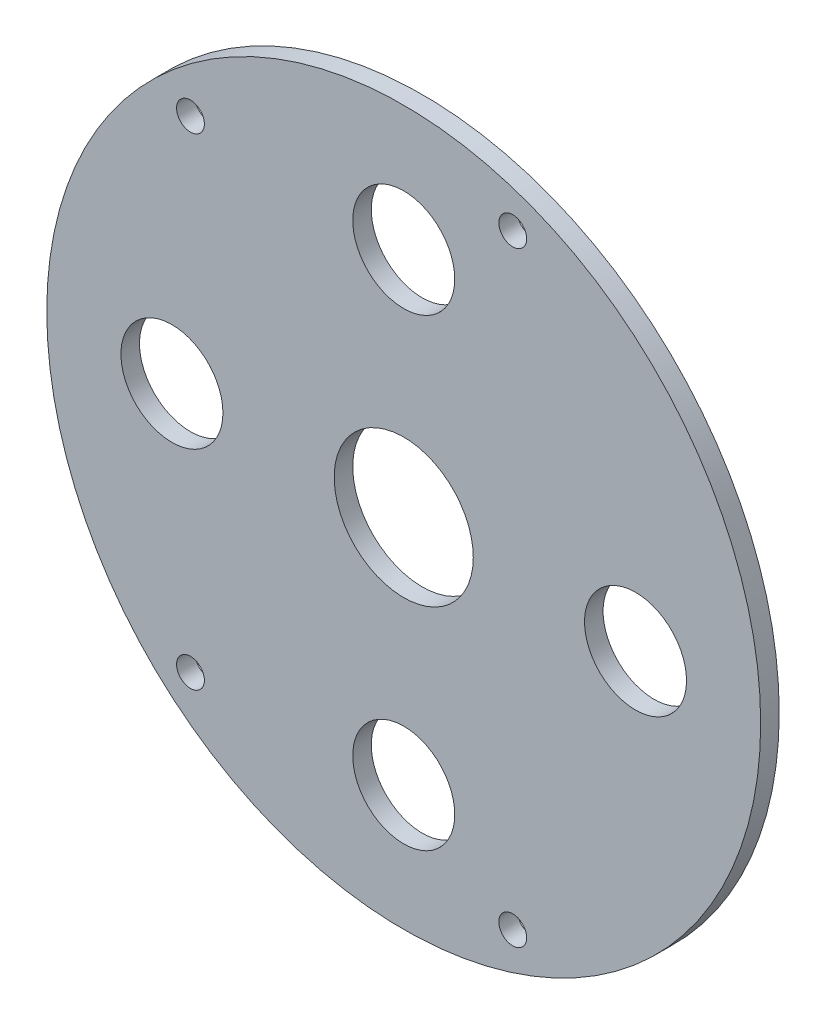
SolidWorks part; units mm, degrees
material "Acrylic (Medium-high impact)"
ref_plane "Front Plane" through (0, 0, 0) normal (0, 0, 1) x (1, 0, 0)
ref_plane "Top Plane" through (0, 0, 0) normal (0, 1, 0) x (1, 0, 0)
ref_plane "Right Plane" through (0, 0, 0) normal (1, 0, 0) x (0, 0, -1)
sketch "Model" plane through (0, 0, 0) normal (0, 0, 1) x (1, 0, 0)
  circle A5 centre (0, 0) radius 38.5
  circle A6 centre (-23, 25.98) radius 1.5
  circle A7 centre (11.7571, -32.6461) radius 1.5
  circle A8 centre (11.7571, 32.6461) radius 1.5
  circle A9 centre (-23, -25.98) radius 1.5
  circle A10 centre (-25, 0) radius 5.5
  circle A11 centre (0, 25) radius 5.5
  circle A12 centre (0, -25) radius 5.5
  circle A13 centre (25, 0) radius 5.5
  circle A14 centre (0, 0) radius 7.5
  dimension "D1" = 3
  dimension "D2" = 11
  dimension "D3" = 15
  dimension "D4" = 77
  dimension "D5" = 11.7571
  dimension "D6" = 25
  dimension "D7" = 25
  dimension "D8" = 23
  dimension "D9" = 25.98
  dimension "D10" = 25
  dimension "D11" = 32.6461
  dimension "D12" = 25.98
  dimension "D13" = 25
  dimension "D14" = 32.6461
extrude "Boss-Extrude1" add sketch "Model" along normal blind 2
